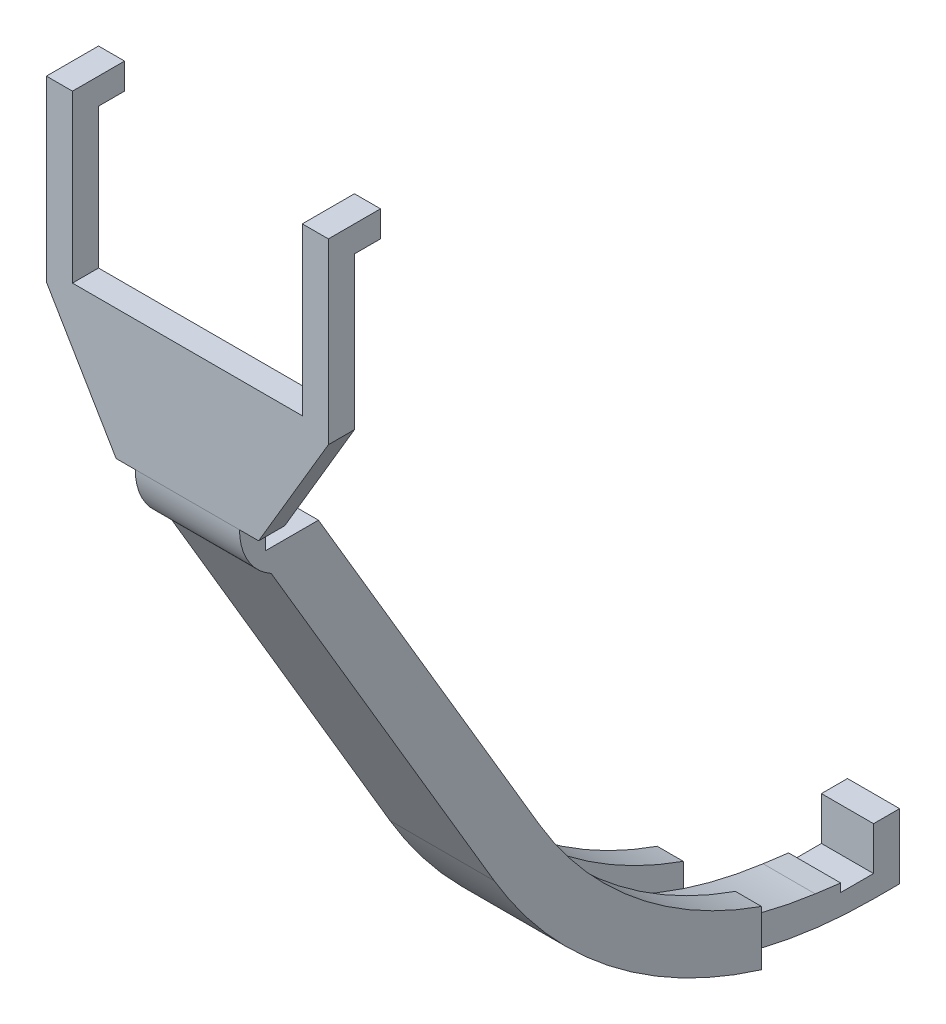
SolidWorks part; units mm, degrees
ref_plane "Front Plane" through (0, 0, 0) normal (0, 0, 1) x (1, 0, 0)
ref_plane "Top Plane" through (0, 0, 0) normal (0, 1, 0) x (1, 0, 0)
ref_plane "Right Plane" through (0, 0, 0) normal (1, 0, 0) x (0, 0, -1)
sketch "Sketch1" plane through (0, 0, 0) normal (0, 1, 0) x (1, 0, 0)
  circle A0 centre (0, 0) radius 30
  dimension "D1" = 60
sketch "Sketch3" plane through (0, 0, 0) normal (1, 0, 0) x (0, 0, -1)
  line L0 (0, 16.1146) -> (0, -58.8622) construction
sketch "Sketch2" plane through (0, 0, 0) normal (1, 0, 0) x (0, 0, -1)
  line L1 (30, 0) -> (-30, 0) construction
  line L2 (0, -50.8) -> (-30, 0)
  line L4 (0, 0) -> (0, -50.8)
  line L5 (-30, 0) -> (0, 0)
  dimension "D1" = 30
revolve "Revolve1" add sketch "Sketch2" angle 360 about L4
sketch "Sketch4" plane through (0, 0, 0) normal (1, 0, 0) x (0, 0, -1)
  line L0 (0, -45.72) -> (-24.92, 0)
  line L1 (0, 16.1146) -> (0, -58.8622) construction
  line L2 (30, 0) -> (-30, 0) construction
  line L3 (-24.92, 0) -> (0, 0)
  line L4 (0, 0) -> (0, -45.72)
  dimension "D1" = 5.08
  dimension "D2" = 5.08
revolve "Cut-Revolve1" cut sketch "Sketch4" angle 360 about L0
sketch "Sketch5" plane through (0, 0, 0) normal (1, 0, 0) x (0, 0, -1)
  line L0 (0, 16.1146) -> (0, -58.8622) construction
  line L1 (6.44, -39.8949) -> (-6.44, -39.8949)
  line L2 (6.44, -39.8949) -> (6.44, -55.7296)
  line L3 (6.44, -55.7296) -> (-6.44, -55.7296)
  line L4 (-6.44, -39.8949) -> (-6.44, -55.7296)
  line L5 (0, -50.8) -> (30, 0) construction
  line L6 (-24.92, 0) -> (0, -45.72) construction
  line L7 (30, 0) -> (-30, 0) construction
  line L8 (0, -45.72) -> (24.92, 0) construction
  point P4 (0, -39.8949)
  point P7 (3.175, -39.8949)
  point P18 (-3.175, -39.8949)
  dimension "D1" = 6.35
  dimension "D2" = 5.08
  dimension "D3" = 5.08
extrude "Cut-Extrude2" cut sketch "Sketch5" against normal mid plane 15.24
ref_plane "Plane1" through (0, 0, 30) normal (0, 0, 1) x (1, 0, 0)
sketch "Sketch11" plane through (0, 0, 30) normal (0, 0, 1) x (1, 0, 0)
  line L0 (30, 0) -> (-30, 0) construction
  line L1 (6.35, 0) -> (3.175, 0)
  line L2 (6.35, 0) -> (6.35, -3.175)
  line L3 (6.35, -3.175) -> (3.175, -3.175)
  line L4 (3.175, 0) -> (3.175, -3.175)
  line L5 (3.175, -3.175) -> (-3.175, -3.175) construction
  line L6 (-3.175, 0) -> (-6.35, 0)
  line L7 (-3.175, 0) -> (-3.175, -3.175)
  line L8 (-3.175, -3.175) -> (-6.35, -3.175)
  line L9 (-6.35, 0) -> (-6.35, -3.175)
  point P10 (0, -3.175)
  dimension "D1" = 3.175
  dimension "D2" = 3.175
  dimension "D3" = 6.35
extrude "Cut-Extrude6" cut sketch "Sketch11" against normal up to next
sketch "Sketch6" plane through (0, 0, 0) normal (1, 0, 0) x (0, 0, -1)
  line L0 (-7.3746, -39.8949) -> (21.4198, -88.6535)
  line L1 (70.8, -110.49) -> (70.8, -108.9025)
  line L2 (70.8, -108.9025) -> (73.975, -108.9025)
  line L3 (73.975, -108.9025) -> (73.975, -116.84)
  line L5 (0, -39.8949) -> (26.8876, -85.4245)
  line L6 (-30, 0) -> (-6.44, -39.8949) construction
  line L7 (30, 0) -> (-30, 0) construction
  line L8 (0, 16.1146) -> (0, -58.8622) construction
  line L11 (0, -39.8949) -> (-23.56, 0)
  line L12 (0, -39.8949) -> (-7.3746, -39.8949)
  line L13 (-23.56, 0) -> (-30.9346, 0)
  line L14 (-7.3746, -39.8949) -> (-30.9346, 0)
  line L15 (-6.44, -39.8949) -> (6.44, -39.8949) construction
  line L16 (70.8, -116.84) -> (73.975, -116.84)
  arc A0 (21.4198, -88.6535) -> (50.8, -113.2395) centre (70.8, -59.492) ccw
  arc A1 (26.8876, -85.4245) -> (70.8, -110.49) centre (70.8, -59.492) ccw
  arc A2 (50.8, -113.2395) -> (70.8, -116.84) centre (70.8, -59.492) ccw
  dimension "D1" = 3.175
  dimension "D3" = 1.5875
  dimension "D2" = 6.35
  dimension "D4" = 6.35
  dimension "D5" = 116.84
  dimension "D6" = 50.8
  dimension "D7" = 20
extrude "Boss-Extrude1" add sketch "Sketch6" along normal mid plane 12.7
sketch "Sketch7" plane through (0, 0, 0) normal (1, 0, 0) x (0, 0, -1)
  line L0 (-3.175, -39.8949) -> (24.5335, -86.8147)
  line L1 (26.8876, -85.4245) -> (0, -39.8949) construction
  line L2 (0, 16.1146) -> (0, -58.8622) construction
  line L3 (-3.175, -39.8949) -> (-26.735, 0)
  line L4 (30, 0) -> (-30, 0) construction
  line L5 (-1.0729, -39.8949) -> (0, -39.8949) construction
  line L8 (-23.56, 0) -> (-26.735, 0)
  line L9 (26.8876, -85.4245) -> (-23.56, 0)
  line L10 (70.8, -113.665) -> (70.8, -110.49)
  arc A0 (24.5335, -86.8147) -> (63.693, -112.7518) centre (70.8, -59.492) ccw
  arc A1 (26.8876, -85.4245) -> (70.8, -110.49) centre (70.8, -59.492) ccw construction
  arc A4 (26.8876, -85.4245) -> (40.4224, -100.4553) centre (70.8, -59.492) ccw
  arc A7 (63.693, -112.7518) -> (70.8, -113.665) centre (161.1847, 617.854) ccw
  arc A8 (26.8876, -85.4245) -> (70.8, -110.49) centre (70.8, -59.492) ccw construction
  arc A9 (70.8, -110.49) -> (40.4224, -100.4553) centre (70.8, -59.492) cw
  dimension "D1" = 3.175
  dimension "D2" = 3.175
extrude "Cut-Extrude4" cut sketch "Sketch7" against normal blind 3.175 contours L0 A0 A7 L10 A9 A4 L9 L8 L3
mirror "Mirror1" about plane through (0, 0, 0) normal (1, 0, 0) of "Cut-Extrude4"
sketch "Sketch9" plane through (0, 0, 0) normal (1, 0, 0) x (0, 0, -1)
  line L0 (0, 0) -> (-24.92, 0)
  line L1 (-24.92, 0) -> (-0.5365, -39.8949)
  line L2 (-1.0729, -39.8949) -> (0, -39.8949) construction
  line L3 (-0.5365, -39.8949) -> (0, -39.8949)
  line L4 (0, -39.8949) -> (0, 0)
  dimension "D1" = 24.92
revolve "Cut-Revolve2" cut sketch "Sketch9" angle 360 about L0
sketch "Sketch10" plane through (-6.35, 0, 0) normal (-1, 0, 0) x (0, 0, 1)
  line L0 (-70.8, -110.49) -> (-70.8, -108.9025) construction
  line L1 (-70.8, -110.3329) -> (-66.8, -110.3329)
  line L2 (-70.8, -110.3329) -> (-70.8, -113.665)
  line L3 (-70.8, -113.665) -> (-66.8, -113.665)
  line L4 (-66.8, -110.3329) -> (-66.8, -113.665)
  line L6 (-70.8, -113.665) -> (-66.8, -113.665)
  line L7 (-70.8, -113.665) -> (-70.8, -114.165)
  line L8 (-70.8, -114.165) -> (-66.8, -114.165)
  line L9 (-66.8, -113.665) -> (-66.8, -114.165)
  arc A0 (-70.8, -110.49) -> (-26.8876, -85.4245) centre (-70.8, -59.492) ccw construction
  arc M9 (-26.8876, -85.4245) -> (-70.8, -110.49) centre (-70.8, -59.492) cw
  dimension "D1" = 0.5
  dimension "D2" = 4
extrude "Cut-Extrude5" cut sketch "Sketch10" against normal through all contours L4 L2 L3 M9 | L9 L3 L7 L8
sketch "Sketch12" plane through (0, 0, 0) normal (-1, 0, 0) x (0, 0, 1)
  line L1 (30, 0) -> (-61.0259, 0)
  line L2 (-61.0259, 0) -> (-61.0259, -39.8949)
  line L6 (30, 0) -> (-30, 0) construction
  line L7 (29.3203, 0) -> (30.9346, 0) construction
  line L9 (-6.44, -39.8949) -> (-61.0259, -39.8949)
  line L10 (27.9452, -3.175) -> (6.44, -39.8949)
  line L11 (27.9452, -3.175) -> (30, 0)
  line L12 (-6.44, -39.8949) -> (6.44, -39.8949)
  line L13 (0, 16.1146) -> (0, -58.8622) construction
  dimension "D1" = 30
  dimension "D2" = 6.44
extrude "Cut-Extrude7" cut sketch "Sketch12" against normal mid plane 81.28
sketch "Sketch13" plane through (0, -13.5447, 22.9358) normal (0, -0.5085, 0.8611) x (1, 0, 0)
  line L1 (-6.35, 15.7303) -> (-28.6819, 15.7303)
  line L2 (-6.35, 15.7303) -> (-6.35, -41.1116)
  line L3 (-6.35, -41.1116) -> (-28.6819, -41.1116)
  line L4 (-28.6819, 15.7303) -> (-28.6819, -41.1116)
  line L5 (6.35, 15.7303) -> (27.8907, 15.7303)
  line L6 (6.35, 15.7303) -> (6.35, -42.7196)
  line L7 (6.35, -42.7196) -> (27.8907, -42.7196)
  line L8 (27.8907, 15.7303) -> (27.8907, -42.7196)
extrude "Cut-Extrude8" [suppressed] cut sketch "Sketch13" against normal through all
sketch "Sketch18" plane through (-6.35, 0, 0) normal (-1, 0, 0) x (0, 0, 1)
  line L0 (6.44, -39.8949) -> (6.44, 0)
  line L1 (30, 0) -> (-30, 0) construction
  line L2 (6.44, 0) -> (9.615, 0)
  line L3 (9.615, 0) -> (9.615, -34.4736)
  line L4 (27.9452, -3.175) -> (6.44, -39.8949) construction
  line L6 (9.615, -34.4736) -> (9.615, -36.1012)
  line L7 (-21.4198, -88.6535) -> (30.9346, 0) construction
  line L8 (5.7568, -42.6345) -> (6.44, -41.4775)
  line L9 (6.44, -41.4775) -> (6.44, -39.8949)
  arc A1 (9.615, -36.1012) -> (5.7568, -42.6345) centre (2.1544, -36.1012) cw
  point P14 (8.5784, -39.8949)
  dimension "D1" = 3.175
extrude "Boss-Extrude3" add sketch "Sketch18" against normal up to surface (12.7 mm away) up to face at (6.35, -75.6156, -31.4396)
sketch "Sketch19" plane through (-6.35, 0, 0) normal (-1, 0, 0) x (0, 0, 1)
  line L0 (9.615, 0) -> (9.615, -36.1012)
  line L1 (9.615, -36.1012) -> (30.9346, -36.1012)
  line L2 (30.9346, -36.1012) -> (30.9346, 0)
  line L3 (30.9346, 0) -> (9.615, 0)
  line L4 (-21.4198, -88.6535) -> (5.7568, -42.6345) construction
extrude "Cut-Extrude10" cut sketch "Sketch19" against normal through all
sketch "Sketch21" plane through (0, 0, 9.615) normal (0, 0, 1) x (1, 0, 0)
  line L1 (-6.35, 0) -> (-15.5875, 0)
  line L2 (-6.35, 0) -> (-6.35, -3.175)
  line L3 (-6.35, -3.175) -> (-15.5875, -3.175)
  line L4 (-15.5875, 0) -> (-15.5875, -3.175)
  line L5 (6.35, 0) -> (15.5875, 0)
  line L6 (6.35, 0) -> (6.35, -3.175)
  line L7 (6.35, -3.175) -> (15.5875, -3.175)
  line L8 (15.5875, 0) -> (15.5875, -3.175)
  line L9 (-15.5875, -3.175) -> (-6.35, -3.175)
  line L10 (-15.5875, -3.175) -> (-15.5875, -36.1012)
  line L11 (-15.5875, -36.1012) -> (-6.35, -36.1012)
  line L12 (-6.35, -3.175) -> (-6.35, -36.1012)
  line L13 (15.5875, -3.175) -> (6.35, -3.175)
  line L14 (15.5875, -3.175) -> (15.5875, -36.1012)
  line L15 (15.5875, -36.1012) -> (6.35, -36.1012)
  line L16 (6.35, -3.175) -> (6.35, -36.1012)
  line M9 (-6.35, 0) -> (-6.35, -36.1012)
  line M11 (6.35, -36.1012) -> (6.35, 0)
  dimension "D1" = 31.175
  dimension "D2" = 3.175
extrude "Boss-Extrude4" add sketch "Sketch21" against normal up to surface (3.175 mm away) contours L10 L11 L3 M9 | L15 L14 L7 M11 | L8 L5 L7 M11 | L1 L4 L3 M9 up to face at (0, -19.9475, 6.44)
sketch "Sketch15" plane through (-15.5875, 0, 0) normal (-1, 0, 0) x (0, 0, 1)
  line L0 (9.615, 0) -> (3.265, 0)
  line L1 (30, 0) -> (-30, 0) construction
  line L2 (3.265, 0) -> (3.265, -3.175)
  line L3 (3.265, -3.175) -> (9.615, -3.175)
  line L5 (9.615, -3.175) -> (9.615, 0)
  line L7 (9.615, -36.1012) -> (9.615, 0) construction
  dimension "D1" = 3.175
  dimension "D2" = 6.35
extrude "Boss-Extrude2" add sketch "Sketch15" along normal mid plane 3.175
mirror "Mirror2" about plane through (0, 0, 0) normal (1, 0, 0) of "Boss-Extrude2"
sketch "Sketch16" [suppressed] plane through (0, 0, 0) normal (0, 1, 0) x (1, 0, 0)
  line L0 (7.9375, -28.9309) -> (7.9375, -30.9346)
  line L1 (7.9375, -9.615) -> (7.9375, -3.265) construction
  line L2 (7.9375, -30.9346) -> (-7.9375, -30.9346)
  line L3 (-7.9375, -30.9346) -> (-7.9375, -28.9309)
  circle A0 centre (0, 0) radius 30
  circle A1 centre (0, 0) radius 30 construction
sketch "Sketch17" plane through (0, 0, -73.975) normal (0, 0, -1) x (-1, 0, 0)
  line L0 (-6.35, -85.4245) -> (-6.35, -110.3329) construction
  line L1 (-6.35, -70.6178) -> (-3.175, -70.6178)
  line L2 (-6.35, -70.6178) -> (-6.35, -116.84)
  line L3 (-6.35, -116.84) -> (-3.175, -116.84)
  line L4 (-3.175, -70.6178) -> (-3.175, -116.84)
  line L5 (-6.35, -116.84) -> (6.35, -116.84) construction
  line L6 (3.175, -85.4245) -> (3.175, -110.3329) construction
  line L7 (3.175, -70.6178) -> (6.35, -70.6178)
  line L8 (3.175, -70.6178) -> (3.175, -116.84)
  line L9 (3.175, -116.84) -> (6.35, -116.84)
  line L10 (6.35, -70.6178) -> (6.35, -116.84)
  line L11 (-3.175, -110.3329) -> (-3.175, -85.4245) construction
extrude "Cut-Extrude9" cut sketch "Sketch17" against normal blind 20
sketch "Sketch20" plane through (0, 0, 0) normal (0, 1, 0) x (1, 0, 0)
  line L0 (-3.175, 26.8876) -> (-3.175, 53.975) construction
  line L1 (3.175, 74.61) -> (-3.175, 74.61)
  line L2 (3.175, 74.61) -> (3.175, 70.61)
  line L3 (3.175, 70.61) -> (-3.175, 70.61)
  line L4 (-3.175, 74.61) -> (-3.175, 70.61)
  dimension "D1" = 4
sketch "Sketch22" plane through (0, 0, 9.615) normal (0, 0, 1) x (1, 0, 0)
  line L0 (17.175, 0) -> (-17.175, 0) construction
  line L1 (14, 0) -> (-14, 0)
  line L2 (14, 0) -> (14, -20.25)
  line L3 (14, -20.25) -> (-14, -20.25)
  line L4 (-14, 0) -> (-14, -20.25)
  point P7 (0, 0)
  point P8 (0, 0)
  dimension "D1" = 28
  dimension "D2" = 20.25
extrude "Cut-Extrude11" cut sketch "Sketch22" against normal through all
sketch "Sketch23" plane through (0, 0, 9.615) normal (0, 0, 1) x (1, 0, 0)
  line L0 (15.5875, -36.1012) -> (6.35, -36.1012) construction
  line L1 (-17.175, -3.175) -> (-15.5875, -3.175)
  line L2 (-17.175, -3.175) -> (-17.175, -36.1012)
  line L3 (-17.175, -36.1012) -> (-15.5875, -36.1012)
  line L4 (-15.5875, -3.175) -> (-15.5875, -36.1012)
  line L5 (17.175, -3.175) -> (15.5875, -3.175)
  line L6 (17.175, -3.175) -> (17.175, -36.1012)
  line L7 (17.175, -36.1012) -> (15.5875, -36.1012)
  line L8 (15.5875, -3.175) -> (15.5875, -36.1012)
extrude "Boss-Extrude5" add sketch "Sketch23" against normal up to surface (3.175 mm away) up to face at (0, -23.1162, 6.44)
sketch "Sketch24" plane through (0, 0, 30) normal (0, 0, 1) x (1, 0, 0)
  line L0 (-17.175, -36.1012) -> (-8.6804, -36.1012)
  line L2 (-8.6804, -36.1012) -> (-17.175, -21.717)
  line L3 (-17.175, -21.717) -> (-17.175, -36.1012)
  line L4 (-17.175, -36.1012) -> (-6.35, -36.1012) construction
  line L5 (-17.175, -36.1012) -> (-17.175, 0) construction
  line L6 (17.175, -21.717) -> (17.175, -36.1012)
  line L7 (17.175, -36.1012) -> (17.175, 0) construction
  line L8 (17.175, -36.1012) -> (8.6804, -36.1012)
  line L9 (17.175, -36.1012) -> (6.35, -36.1012) construction
  line L10 (8.6804, -36.1012) -> (17.175, -21.717)
  dimension "D1" = 8.4946
  dimension "D2" = 14.3842
extrude "Cut-Extrude12" cut sketch "Sketch24" against normal through all
